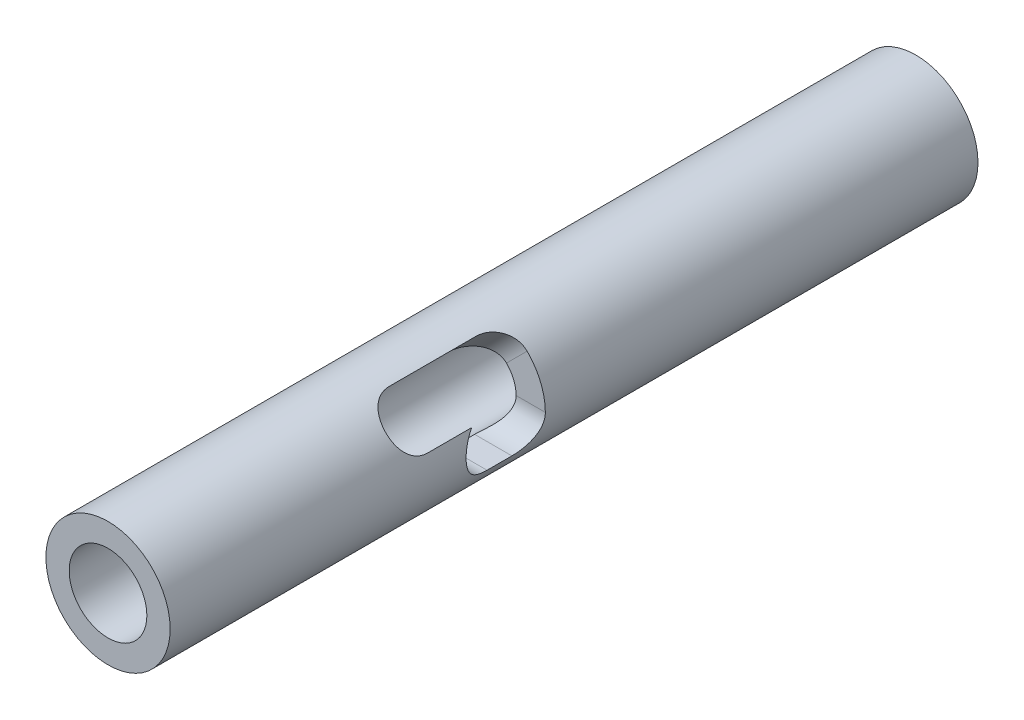
SolidWorks part; units mm, degrees
material "6061 Alloy"
ref_plane "Front Plane" through (0, 0, 0) normal (0, 0, 1) x (1, 0, 0)
ref_plane "Top Plane" through (0, 0, 0) normal (0, 1, 0) x (1, 0, 0)
ref_plane "Right Plane" through (0, 0, 0) normal (1, 0, 0) x (0, 0, -1)
sketch "Sketch51" plane through (0, 0, 0) normal (0, 1, 0) x (1, 0, 0)
  line L0 (0, 0) -> (0, 2.4601) construction
sketch "Sketch1" plane through (0, 0, 0) normal (0, 0, 1) x (1, 0, 0)
  circle A0 centre (0, 0) radius 6.35
  circle A1 centre (0, 0) radius 3.3655
  dimension "D1" = 12.7
  dimension "D2" = 6.731
extrude "Boss-Extrude1" add sketch "Sketch1" along normal blind 82.55
hole_wizard "3/8-16 Tapped Hole0" positions "3DSketch3" profile "Sketch8" tap size "3/8-16" standard "ANSI Inch"
sketch3d "3DSketch3"
  point P0 (0, 0, 0)
sketch "Sketch8" plane through (0, 0, 0) normal (1, 0, 0) x (0, 1, 0)
  line L0 (0, 0) -> (0, 21.4347)
  line L1 (0, 21.4347) -> (3.9687, 19.05)
  line L2 (3.9687, 19.05) -> (3.9687, 0)
  line L5 (3.9687, 0) -> (0, 0)
  line L10 (0, 21.4347) -> (-3.9688, 19.05) construction
  line L11 (0, -6.35) -> (0, 107.95) construction
  dimension "Tap Drill Dia." = 7.9375
  dimension "Tap Drill Depth" = 19.05
  dimension "Drill Angle" = 118
cosmetic thread "Hole Thread1" parameters "D1"=12.7, "D2"=9.525
ref_plane "Plane2" through (0, 0, 49.53) normal (0, 0, 1) x (1, 0, 0)
sketch "Sketch12" plane through (0, 0, 49.53) normal (0, 0, 1) x (1, 0, 0)
  line L0 (0, 0) -> (8.9803, 8.9803) construction
  line L1 (0, 0) -> (12.7, 0) construction
  line L2 (0, 0) -> (11.7333, 4.8601) construction
  circle A0 centre (0, 0) radius 6.35 construction
  arc A1 (6.35, 0) -> (4.4901, 4.4901) centre (0, 0) ccw
  point P2 (5.8666, 2.43)
  dimension "D1" = 12.7
  dimension "D2" = 12.7
  dimension "D3" = 45
  dimension "D4" = 12.7
  dimension "D5" = 22.5
sketch "Sketch13" plane through (0, 0, 0) normal (1, 0, 0) x (0, 0, -1)
  line L0 (-49.53, 0) -> (-46.99, 0) construction
  line L3 (-49.53, 2.7781) -> (-46.99, 2.7781)
  line L4 (-49.53, -2.7781) -> (-46.99, -2.7781)
  arc A3 (-49.53, 2.7781) -> (-49.53, -2.7781) centre (-49.53, 0) ccw
  arc A4 (-46.99, -2.7781) -> (-46.99, 2.7781) centre (-46.99, 0) ccw
  point P0 (-49.53, 0)
  point P4 (-48.26, 0)
  dimension "D1" = 2.54
  dimension "D2" = 2.7781
extrude "Cut-Extrude2" cut sketch "Sketch13" along normal through all
ref_plane "Plane3" through (0, 0, 0) normal (0.7071, 0.7071, 0) x (0.7071, -0.7071, 0)
sketch "Sketch75" plane through (0, 0, 0) normal (0, 1, 0) x (1, 0, 0)
  line L0 (0, -49.53) -> (12.7, -49.53)
  line L9 (12.7, -49.53) -> (12.7, -44.2119)
  line L10 (12.7, -44.2119) -> (0, -44.2119)
  line L11 (0, -44.2119) -> (0, -49.53)
  dimension "D1" = 5.3181
revolve "Cut-Revolve1" cut sketch "Sketch75" angle 45 about L0
sketch "Sketch52" plane through (0, 0, 0) normal (0.7071, 0.7071, 0) x (0.7071, -0.7071, 0)
  line L0 (0, -55.88) -> (0, -46.99) construction
  line L3 (-2.7781, -55.88) -> (-2.7781, -46.99)
  line L4 (2.7781, -55.88) -> (2.7781, -46.99)
  line L5 (0, -49.53) -> (8.9803, -49.53) construction
  arc A2 (-2.7781, -55.88) -> (2.7781, -55.88) centre (0, -55.88) ccw
  arc A3 (2.7781, -46.99) -> (-2.7781, -46.99) centre (0, -46.99) ccw
  point P2 (0, -51.435)
  dimension "D2" = 6.35
  dimension "D3" = 2.7781
  dimension "D1" = 2.54
extrude "Cut-Extrude3" cut sketch "Sketch52" along normal through all
hole_wizard "3/8-16 Tapped Hole1" positions "3DSketch4" profile "Sketch76" tap size "3/8-16" standard "ANSI Inch"
sketch3d "3DSketch4"
  point P0 (0, 0, 82.55)
sketch "Sketch76" plane through (0, 0, 82.55) normal (1, 0, 0) x (0, -1, 0)
  line L0 (0, 0) -> (0, 21.4347)
  line L1 (0, 21.4347) -> (3.9687, 19.05)
  line L2 (3.9687, 19.05) -> (3.9687, 0)
  line L5 (3.9687, 0) -> (0, 0)
  line L10 (0, 21.4347) -> (-3.9688, 19.05) construction
  line L11 (0, -6.35) -> (0, 107.95) construction
  dimension "Tap Drill Dia." = 7.9375
  dimension "Tap Drill Depth" = 19.05
  dimension "Drill Angle" = 118
cosmetic thread "Hole Thread3" parameters "D1"=12.7, "D2"=9.525
